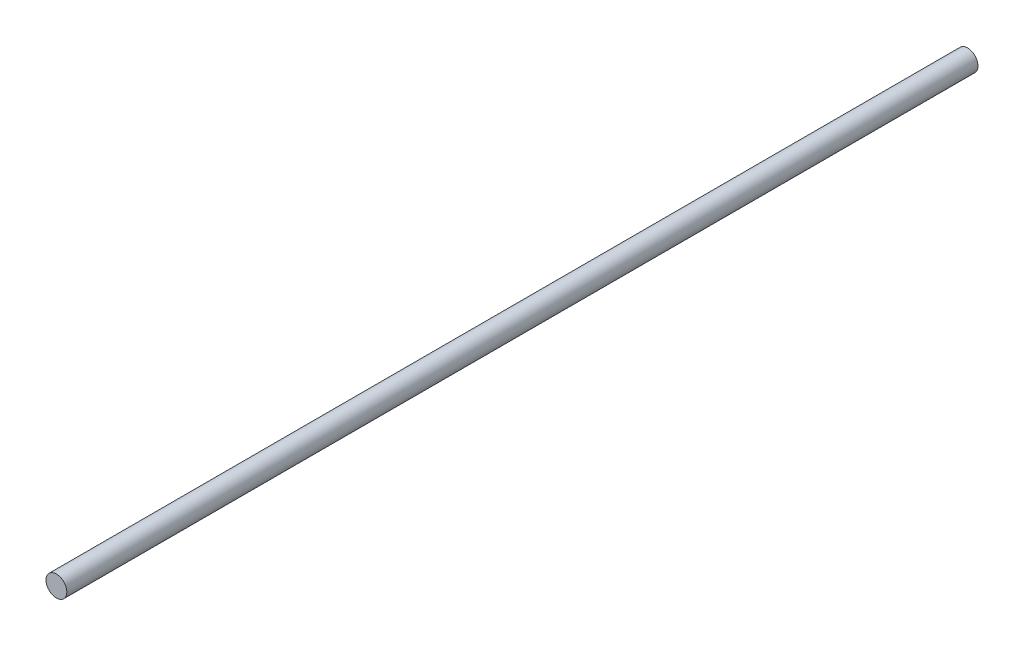
SolidWorks part; units mm, degrees
ref_plane "Plan de face" through (0, 0, 0) normal (0, 0, 1) x (1, 0, 0)
ref_plane "Plan de dessus" through (0, 0, 0) normal (0, 1, 0) x (1, 0, 0)
ref_plane "Plan de droite" through (0, 0, 0) normal (1, 0, 0) x (0, 0, -1)
sketch "Esquisse1" plane through (0, 0, 0) normal (0, 0, 1) x (1, 0, 0)
  circle A0 centre (0, 0) radius 4
  dimension "D1" = 8
extrude "Boss.-Extru.1" add sketch "Esquisse1" along normal blind 350
